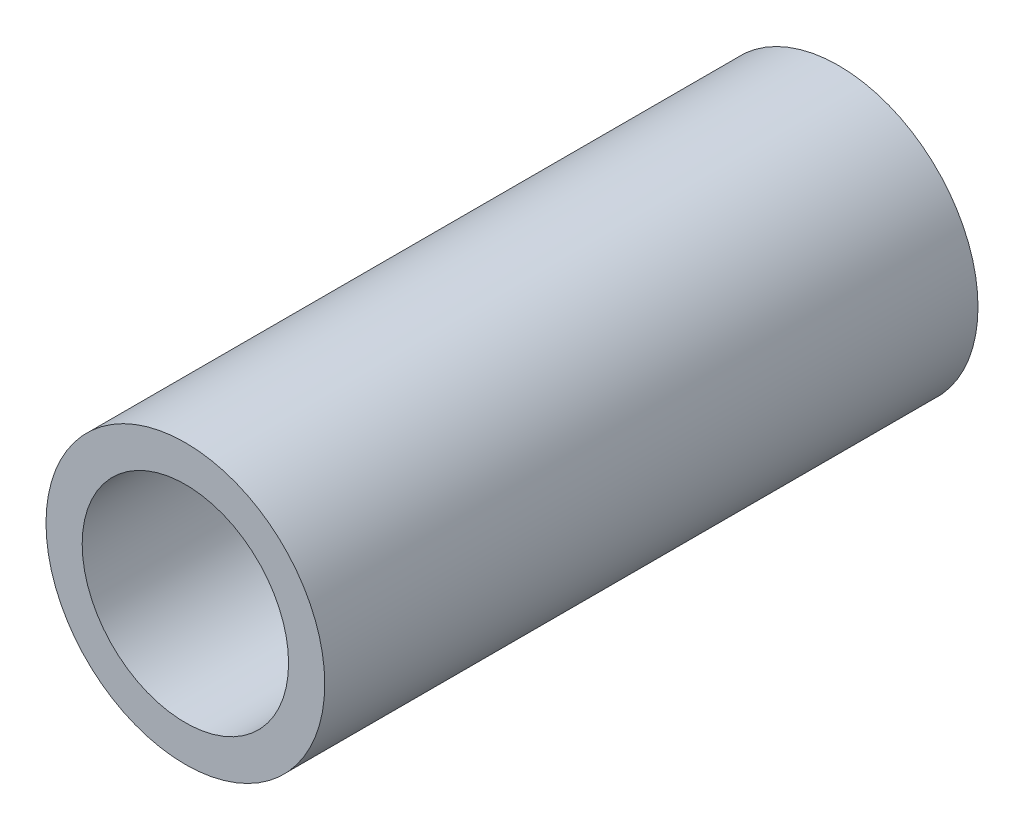
SolidWorks part; units mm, degrees
ref_plane "Front Plane" through (0, 0, 0) normal (0, 0, 1) x (1, 0, 0)
ref_plane "Top Plane" through (0, 0, 0) normal (0, 1, 0) x (1, 0, 0)
ref_plane "Right Plane" through (0, 0, 0) normal (1, 0, 0) x (0, 0, -1)
sketch "Sketch1" plane through (0, 0, 0) normal (0, 0, 1) x (1, 0, 0)
  circle A0 centre (0, 0) radius 10.668
  dimension "Pipe OD" = 21.336
extrude "Extrude-Thin1" add sketch "Sketch1" along normal mid plane 50 thin thin type one direction reverse wall 2.7686
